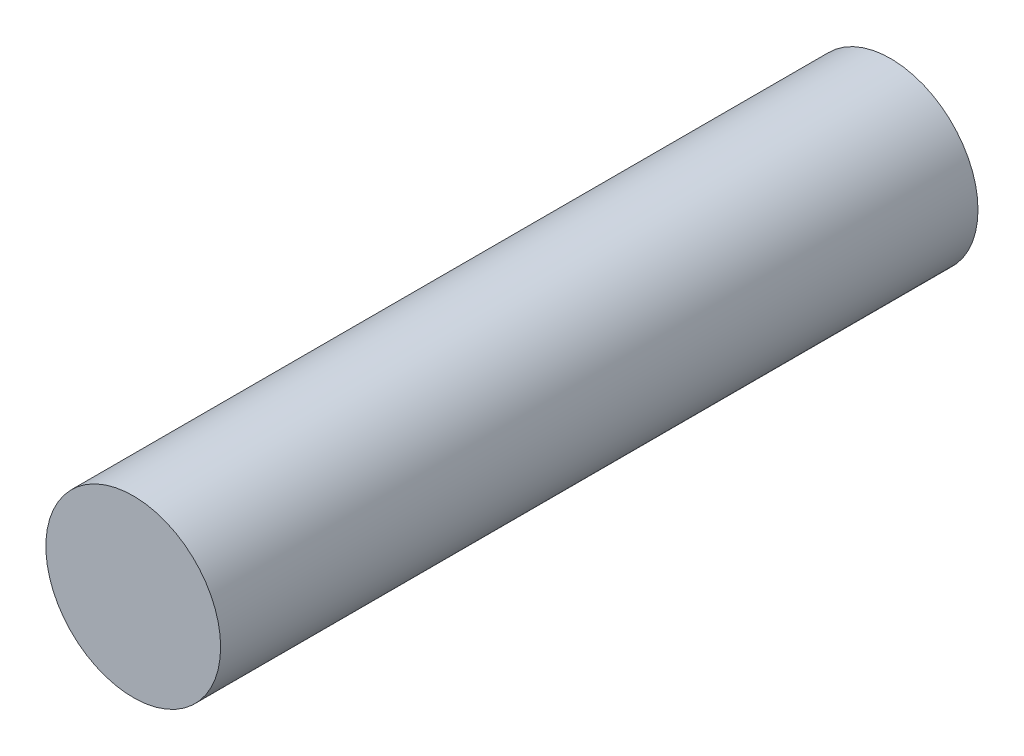
SolidWorks part; units mm, degrees
ref_plane "Спереди" through (0, 0, 0) normal (0, 0, 1) x (1, 0, 0)
ref_plane "Сверху" through (0, 0, 0) normal (0, 1, 0) x (1, 0, 0)
ref_plane "Справа" through (0, 0, 0) normal (1, 0, 0) x (0, 0, -1)
sketch "Эскиз1" plane through (0, 0, 0) normal (0, 0, 1) x (1, 0, 0)
  circle A0 centre (0, 0) radius 2.25
  dimension "D1" = 4.5
extrude "Бобышка-Вытянуть1" add sketch "Эскиз1" along normal blind 19.5
